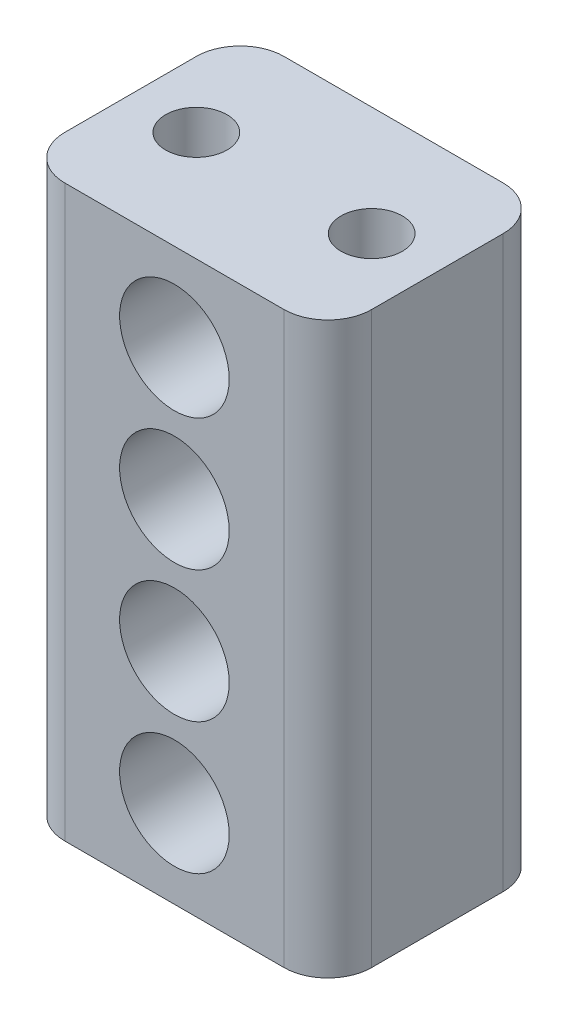
SolidWorks part; units mm, degrees
ref_plane "Front Plane" through (0, 0, 0) normal (0, 0, 1) x (1, 0, 0)
ref_plane "Top Plane" through (0, 0, 0) normal (0, 1, 0) x (1, 0, 0)
ref_plane "Right Plane" through (0, 0, 0) normal (1, 0, 0) x (0, 0, -1)
sketch "Sketch2" plane through (0, 0, 0) normal (0, 0, 1) x (1, 0, 0)
  line L0 (0, 6.5) -> (0, -6.5) construction
  line L1 (-3.5, 6.5) -> (3.5, 6.5)
  line L2 (-3.5, 6.5) -> (-3.5, -6.5)
  line L3 (-3.5, -6.5) -> (3.5, -6.5)
  line L4 (3.5, 6.5) -> (3.5, -6.5)
  line L5 (-3.5, 6.5) -> (3.5, -6.5) construction
  line L6 (-3.5, -6.5) -> (3.5, 6.5) construction
  line L7 (-3.5, 0) -> (3.5, 0) construction
  circle A1 centre (0, 4.5) radius 1.25
  circle A2 centre (3, 4.5) radius 1.25 construction
  circle A3 centre (6, 4.5) radius 1.25 construction
  circle A4 centre (9, 4.5) radius 1.25 construction
  circle A5 centre (3, 1.5) radius 1.25 construction
  circle A6 centre (6, 1.5) radius 1.25 construction
  circle A7 centre (9, 1.5) radius 1.25 construction
  circle A8 centre (3, -1.5) radius 1.25 construction
  circle A9 centre (6, -1.5) radius 1.25 construction
  circle A10 centre (9, -1.5) radius 1.25 construction
  circle A11 centre (3, -4.5) radius 1.25 construction
  circle A12 centre (6, -4.5) radius 1.25 construction
  circle A13 centre (9, -4.5) radius 1.25 construction
  circle A14 centre (0, 1.5) radius 1.25
  circle A15 centre (0, -1.5) radius 1.25
  circle A16 centre (0, -4.5) radius 1.25
  circle A17 centre (-3, 4.5) radius 1.25 construction
  circle A18 centre (-6, 4.5) radius 1.25 construction
  circle A19 centre (-3, 1.5) radius 1.25 construction
  circle A20 centre (-6, 1.5) radius 1.25 construction
  circle A21 centre (-3, -1.5) radius 1.25 construction
  circle A22 centre (-6, -1.5) radius 1.25 construction
  circle A23 centre (-3, -4.5) radius 1.25 construction
  circle A24 centre (-6, -4.5) radius 1.25 construction
  circle A25 centre (0, 1.5) radius 1.25 construction
  circle A26 centre (0, -1.5) radius 1.25 construction
  circle A27 centre (0, -4.5) radius 1.25 construction
  circle A28 centre (0, 1.5) radius 1 construction
  circle A29 centre (0, -1.5) radius 1 construction
  circle A30 centre (0, 4.5) radius 1 construction
  circle A31 centre (0, -4.5) radius 1 construction
  point P0 (0, 0)
  dimension "D2" = 1.5
  dimension "D6" = 0
  dimension "D3" = 2
  dimension "D1" = 13
  dimension "D11" = 7
  dimension "D12" = 3
  dimension "D13" = 3
  dimension "D7" = 4
  dimension "D8" = 4
  dimension "D9" = 3
  dimension "D10" = 4
extrude "Boss-Extrude1" add sketch "Sketch2" along normal blind 5 contours L4 L1 L2 L3 A24 A23 A22 A21 A20 A19 A18 A17 A16 A15 A14 A13 A12 A11 A10 A9 A8 A7 A6 A5 A4 A3 A2
fillet "Fillet1" radius 1 4 edges at (-3.5, 0, 0) (-3.5, 0, 5) (3.5, 0, 5) (3.5, 0, 0)
sketch "Sketch3" plane through (0, 6.5, 0) normal (0, 1, 0) x (1, 0, 0)
  line L0 (-3.5, -2.5) -> (3.5, -2.5) construction
  line L1 (-3.5, -4) -> (-3.5, -1) construction
  line L2 (3.5, -4) -> (3.5, -1) construction
  line L3 (0, 0) -> (0, -5) construction
  line L4 (-2.5, -5) -> (2.5, -5) construction
  circle A0 centre (-2, -2.5) radius 0.7
  circle A2 centre (2, -2.5) radius 0.7
  dimension "D1" = 1.4
  dimension "D2" = 2
  dimension "D3" = 2
extrude "Cut-Extrude1" cut sketch "Sketch3" against normal blind 3
mirror "Mirror1" about plane through (0, 0, 0) normal (0, 1, 0) of "Cut-Extrude1"
